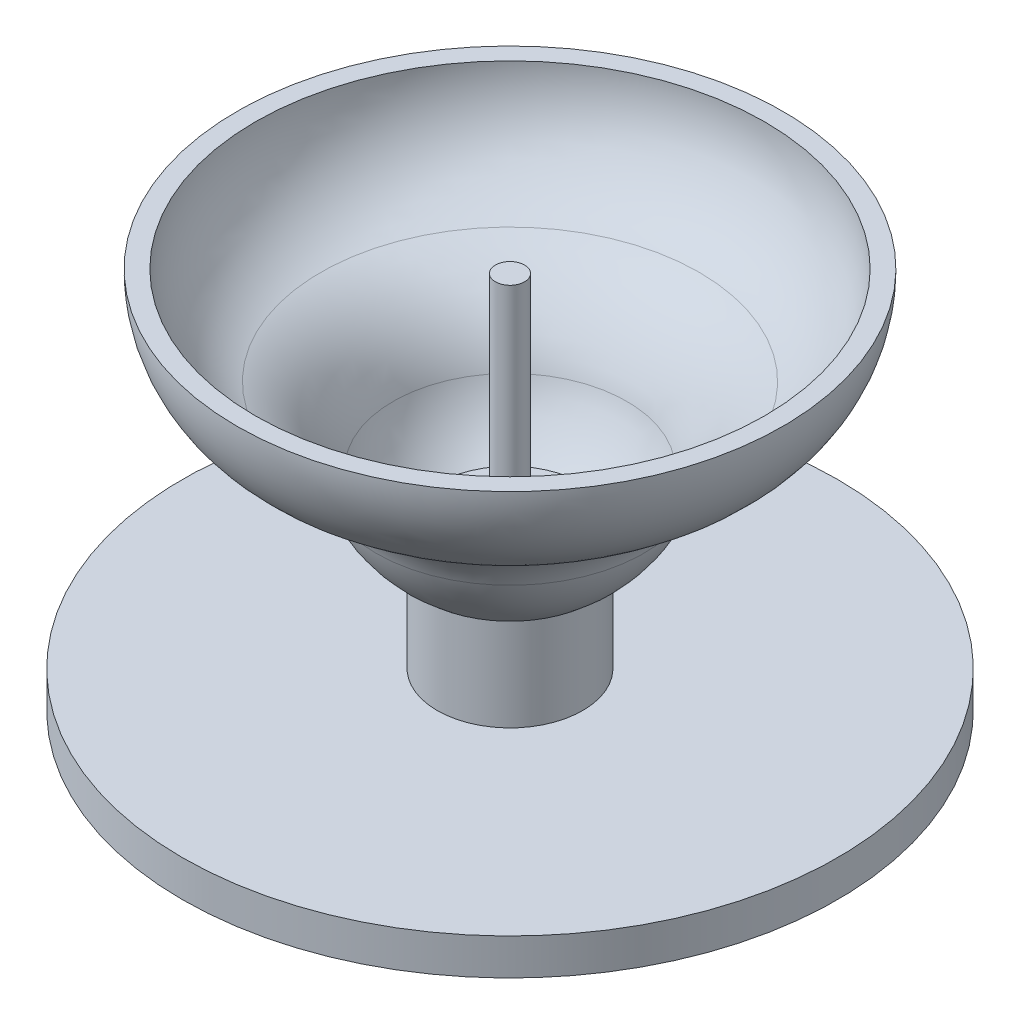
SolidWorks part; units mm, degrees
ref_plane "Plan de face" through (0, 0, 0) normal (0, 0, 1) x (1, 0, 0)
ref_plane "Plan de dessus" through (0, 0, 0) normal (0, 1, 0) x (1, 0, 0)
ref_plane "Plan de droite" through (0, 0, 0) normal (1, 0, 0) x (0, 0, -1)
sketch "Esquisse1" plane through (0, 0, 0) normal (0, 1, 0) x (1, 0, 0)
  circle A0 centre (0, 0) radius 90
  dimension "D1" = 180
extrude "Boss.-Extru.1" add sketch "Esquisse1" along normal blind 10
sketch "Esquisse2" plane through (0, 10, 0) normal (0, 1, 0) x (1, 0, 0)
  circle A0 centre (0, 0) radius 20
  dimension "D1" = 40
extrude "Boss.-Extru.2" add sketch "Esquisse2" along normal blind 93
sketch "Esquisse3" plane through (0, 0, 0) normal (1, 0, 0) x (0, 0, -1)
  line L0 (0, -5.4484) -> (0, 103) construction
  line L2 (-74.9708, 105.0943) -> (-69.9708, 105.0943)
  line L3 (20, 103) -> (-20, 103) construction
  line L4 (0, 103) -> (0, 30)
  line L5 (42.83, 30) -> (-42.83, 30) construction
  line L6 (-74.9708, 105.0943) -> (-74.9708, 140.4054) construction
  line L7 (-69.9708, 105.0943) -> (-69.9708, 119.2286) construction
  line L8 (0, 35) -> (14.583, 35) construction
  line L9 (20, 10) -> (-20, 10) construction
  arc A0 (-74.9708, 105.0943) -> (-53.8936, 73.6441) centre (-40.968, 105.0943) ccw
  arc A1 (-53.8936, 73.6441) -> (-36.8047, 55.814) centre (-65.4918, 45.4237) cw
  arc A2 (-36.8047, 55.814) -> (0, 30) centre (0, 69.1445) ccw
  arc A3 (-69.9708, 105.0943) -> (-51.993, 78.2687) centre (-40.968, 105.0943) ccw
  arc A4 (-51.993, 78.2687) -> (-32.1036, 57.5167) centre (-65.4918, 45.4237) cw
  arc A5 (-32.1036, 57.5167) -> (0, 35) centre (0, 69.1445) ccw
  point P17 (0, 30)
  dimension "D1" = 75
  dimension "D2" = 5
  dimension "D3" = 20
sketch "Esquisse4" plane through (0, 0, 0) normal (0, -1, 0) x (1, 0, 0)
  circle A0 centre (0, 0) radius 36
  circle A1 centre (0, 0) radius 39
  circle A2 centre (0, 0) radius 54
  circle A3 centre (0, 0) radius 57
  circle A4 centre (0, 0) radius 72
  circle A5 centre (0, 0) radius 75
  circle A6 centre (0, 0) radius 90 construction
  dimension "D1" = 3
  dimension "D2" = 3
  dimension "D3" = 3
  dimension "D4" = 15
  dimension "D5" = 15
  dimension "D6" = 15
extrude "Enlèv. mat.-Extru.1" cut sketch "Esquisse4" against normal blind 1 draft 30 contours A5 A4 | A3 A2 | A1 A0
revolve "Révolution2" add sketch "Esquisse3" angle 360 about L4
sketch "Esquisse5" plane through (0, 103, 0) normal (0, 1, 0) x (1, 0, 0)
  circle A0 centre (0, 0) radius 20
extrude "Enlèv. mat.-Extru.2" cut sketch "Esquisse5" against normal blind 59
sketch "Esquisse6" plane through (0, 44, 0) normal (0, 1, 0) x (1, 0, 0)
  circle A0 centre (0, 0) radius 4
  dimension "D1" = 8
extrude "Boss.-Extru.3" add sketch "Esquisse6" along normal blind 60
